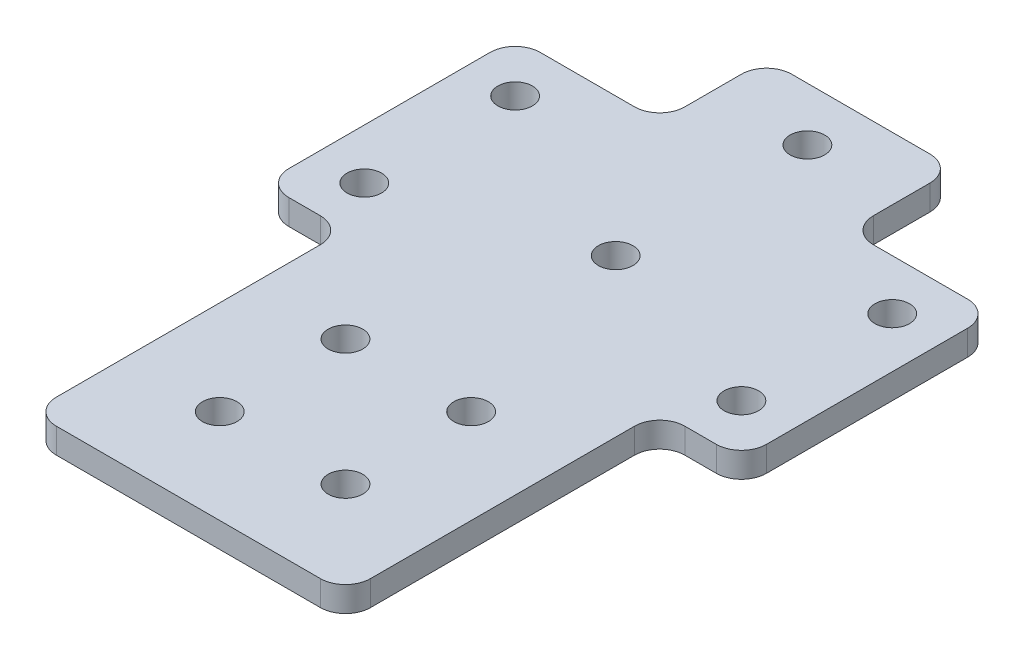
SolidWorks part; units mm, degrees
ref_plane "Front Plane" through (0, 0, 0) normal (0, 0, 1) x (1, 0, 0)
ref_plane "Top Plane" through (0, 0, 0) normal (0, 1, 0) x (1, 0, 0)
ref_plane "Right Plane" through (0, 0, 0) normal (1, 0, 0) x (0, 0, -1)
sketch "Sketch1" plane through (0, 0, 0) normal (0, 1, 0) x (1, 0, 0)
  line L1 (-38, 15) -> (38, 15)
  line L2 (-38, 15) -> (-38, -25)
  line L3 (-38, -25) -> (38, -25)
  line L4 (38, 15) -> (38, -25)
  circle A0 centre (-30, 7) radius 2.75
  circle A1 centre (30, 7) radius 2.75
  circle A2 centre (-30, -17) radius 2.75
  circle A3 centre (30, -17) radius 2.75
  dimension "D5" = 8
  dimension "D13" = 5.5
  dimension "D14" = 5.5
  dimension "D15" = 5.5
  dimension "D16" = 5.5
  dimension "D1" = 76
  dimension "D2" = 38
  dimension "D3" = 15
  dimension "D4" = 40
  dimension "D6" = 8
  dimension "D7" = 8
  dimension "D8" = 8
  dimension "D9" = 60
  dimension "D10" = 30
  dimension "D11" = 30
  dimension "D12" = 60
extrude "Boss-Extrude1" add sketch "Sketch1" along normal blind 4
sketch "Sketch2" plane through (0, 4, 0) normal (0, 1, 0) x (1, 0, 0)
  line L0 (-38, -25) -> (38, -25) construction
  line L1 (-25, -25) -> (25, -25)
  line L2 (-25, -25) -> (-25, -75)
  line L3 (-25, -75) -> (25, -75)
  line L4 (25, -25) -> (25, -75)
  line L5 (-38, 15) -> (-38, -25) construction
  line L6 (38, 15) -> (-38, 15) construction
  line L7 (-15, 15) -> (15, 15)
  line L8 (-15, 15) -> (-15, 32)
  line L9 (-15, 32) -> (15, 32)
  line L10 (15, 15) -> (15, 32)
  dimension "D1" = 50
  dimension "D2" = 13
  dimension "D3" = 50
  dimension "D4" = 30
  dimension "D5" = 23
  dimension "D6" = 17
extrude "Boss-Extrude2" add sketch "Sketch2" against normal blind 4
sketch "Sketch3" plane through (0, 4, 0) normal (0, 1, 0) x (1, 0, 0)
  circle A0 centre (0, 23.5) radius 2.75
  circle A1 centre (0, -7) radius 2.75
  circle A2 centre (-10, -40) radius 2.75
  circle A3 centre (10, -40) radius 2.75
  circle A4 centre (-10, -60) radius 2.75
  circle A5 centre (10, -60) radius 2.75
  dimension "D1" = 5.5
  dimension "D2" = 5.5
  dimension "D3" = 5.5
  dimension "D4" = 5.5
  dimension "D10" = 5.5
  dimension "D11" = 5.5
  dimension "D5" = 20
  dimension "D6" = 20
  dimension "D7" = 10
  dimension "D8" = 15
  dimension "D9" = 30.5
  dimension "D12" = 23.5
extrude "Cut-Extrude1" cut sketch "Sketch3" against normal blind 4
fillet "Fillet1" radius 4 12 edges at (-25, 2, 75) (25, 2, 75) (38, 2, 25) (38, 2, -15) (-38, 2, -15) (-38, 2, 25) (15, 2, -32) (-15, 2, -32)
